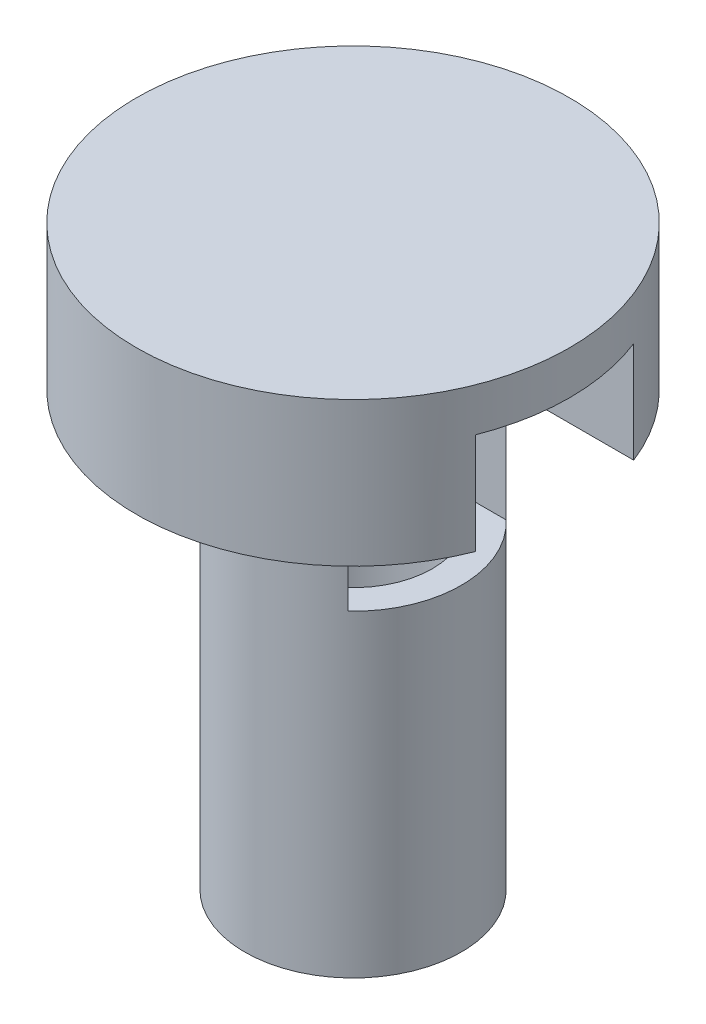
SolidWorks part; units mm, degrees
ref_plane "Front Plane" through (0, 0, 0) normal (0, 0, 1) x (1, 0, 0)
ref_plane "Top Plane" through (0, 0, 0) normal (0, 1, 0) x (1, 0, 0)
ref_plane "Right Plane" through (0, 0, 0) normal (1, 0, 0) x (0, 0, -1)
sketch "Sketch1" plane through (0, 0, 0) normal (0, 1, 0) x (1, 0, 0)
  circle A0 centre (0, 0) radius 19.05
  dimension "D1" = 38.1
extrude "Boss-Extrude1" add sketch "Sketch1" along normal blind 12.7
sketch "Sketch2" plane through (0, 0, 0) normal (0, -1, 0) x (1, 0, 0)
  circle A0 centre (0, 0) radius 9.525
  dimension "D1" = 19.05
extrude "Boss-Extrude2" add sketch "Sketch2" along normal blind 38.1
sketch "Sketch3" plane through (0, -38.1, 0) normal (0, -1, 0) x (1, 0, 0)
  circle A0 centre (0, 0) radius 6.985
  circle A1 centre (0, 0) radius 9.525 construction
  dimension "D1" = 2.54
extrude "Cut-Extrude1" cut sketch "Sketch3" against normal blind 46.99
sketch "Sketch5" plane through (0, 8.89, 0) normal (0, -1, 0) x (1, 0, 0)
  line L0 (0, 0) -> (19.05, 0) construction
  line L1 (0, 6.9571) -> (19.05, 6.9571)
  line L2 (0, -6.9571) -> (19.05, -6.9571)
  circle A0 centre (0, 0) radius 19.05 construction
  arc A1 (0, 6.9571) -> (0, -6.9571) centre (0, 0) ccw
  arc A2 (19.05, -6.9571) -> (19.05, 6.9571) centre (19.05, 0) ccw
  point P5 (9.525, 0)
extrude "Cut-Extrude2" cut sketch "Sketch5" along normal blind 19.05
